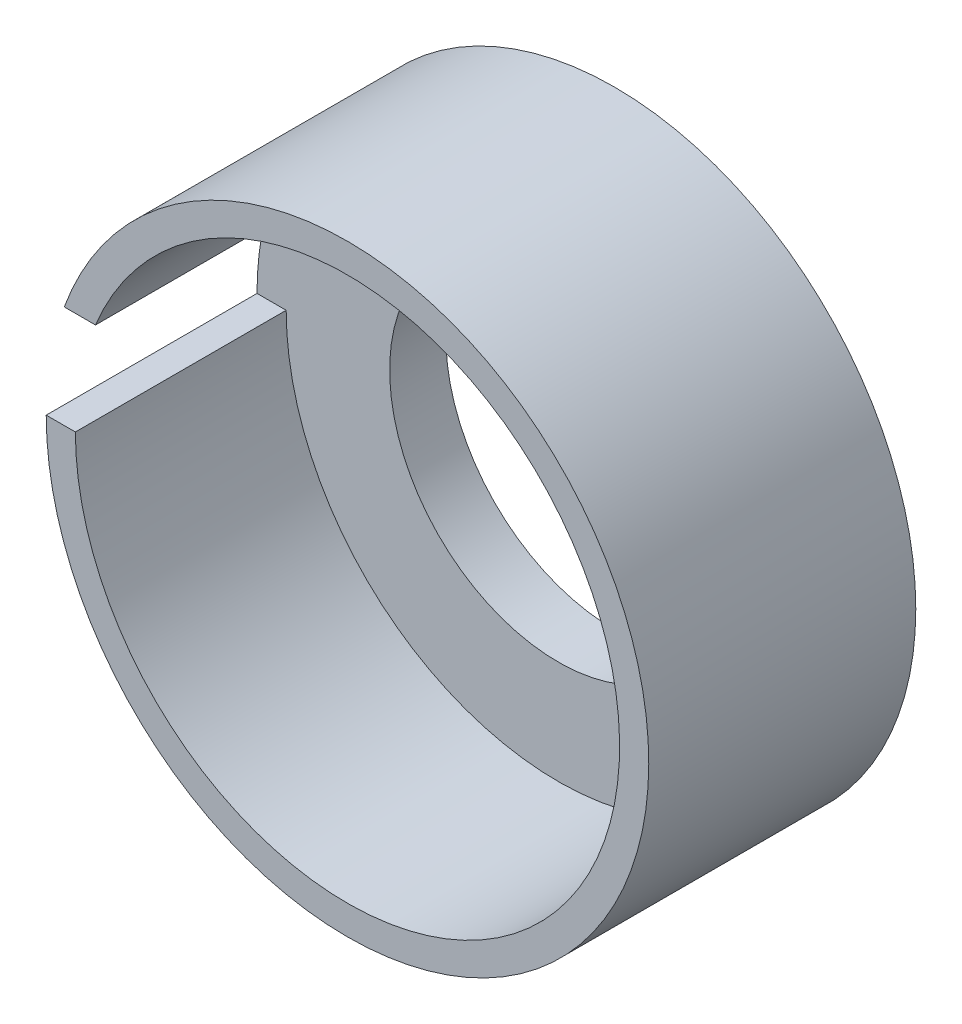
SolidWorks part; units mm, degrees
ref_plane "Front Plane" through (0, 0, 0) normal (0, 0, 1) x (1, 0, 0)
ref_plane "Top Plane" through (0, 0, 0) normal (0, 1, 0) x (1, 0, 0)
ref_plane "Right Plane" through (0, 0, 0) normal (1, 0, 0) x (0, 0, -1)
sketch "Sketch1" plane through (0, 0, 0) normal (0, 0, 1) x (1, 0, 0)
  circle A0 centre (0, 0) radius 38.125
  circle A1 centre (0, 0) radius 42.875
  dimension "D1" = 76.25
  dimension "D2" = 85.75
extrude "Boss-Extrude1" add sketch "Sketch1" along normal blind 8 contours A1
sketch "Sketch2" plane through (0, 0, 8) normal (0, 0, 1) x (1, 0, 0)
  line L0 (-38.725, 0) -> (-42.875, 0)
  line L1 (-35.8608, 14.616) -> (-40.3068, 14.616)
  circle A0 centre (0, 0) radius 38.725
  circle A1 centre (0, 0) radius 42.875 construction
  circle A2 centre (0, 0) radius 42.875
  circle M1 centre (0, 0) radius 42.875
  dimension "D1" = 77.45
  dimension "D2" = 360
extrude "Boss-Extrude2" add sketch "Sketch2" along normal blind 30 contours A0 L0 L1 M1
sketch "Sketch3" plane through (0, 0, 8) normal (0, 0, 1) x (1, 0, 0)
  line L2 (-35.8608, 14.616) -> (-40.3068, 14.616)
  line L3 (-42.875, 0) -> (-38.725, 0)
  line L4 (-35.8608, 14.616) -> (-40.3068, 14.616)
  line L5 (-42.875, 0) -> (-38.725, 0)
  arc A0 (-38.725, 0) -> (-35.8608, 14.616) centre (0, 0) ccw construction
  arc A1 (-42.875, 0) -> (-40.3068, 14.616) centre (0, 0) ccw construction
  arc A2 (-38.725, 0) -> (-35.8608, 14.616) centre (0, 0) ccw
  arc A3 (-42.875, 0) -> (-40.3068, 14.616) centre (0, 0) ccw
  circle A4 centre (0, 0) radius 38.725
  arc A6 (-38.725, 0) -> (-35.8608, 14.616) centre (0, 0) ccw
  arc A7 (-40.3068, 14.616) -> (-42.875, 0) centre (0, 0) ccw
  arc A8 (-38.725, 0) -> (-35.8608, 14.616) centre (0, 0) ccw
  arc A9 (-40.3068, 14.616) -> (-42.875, 0) centre (0, 0) ccw
  line M6 (-35.8608, 14.616) -> (-40.3068, 14.616)
  arc M7 (-40.3068, 14.616) -> (-42.875, 0) centre (0, 0) ccw
  line M8 (-42.875, 0) -> (-38.725, 0)
  dimension "D1" = 0
extrude "Boss-Extrude3" [suppressed] add sketch "Sketch3" along normal blind 6 contours A4 M6 M7 M8
sketch "Sketch4" plane through (0, 0, 8) normal (0, 0, 1) x (1, 0, 0)
  circle A0 centre (0, 0) radius 24
  dimension "D1" = 48
extrude "Cut-Extrude1" cut sketch "Sketch4" against normal blind 20
